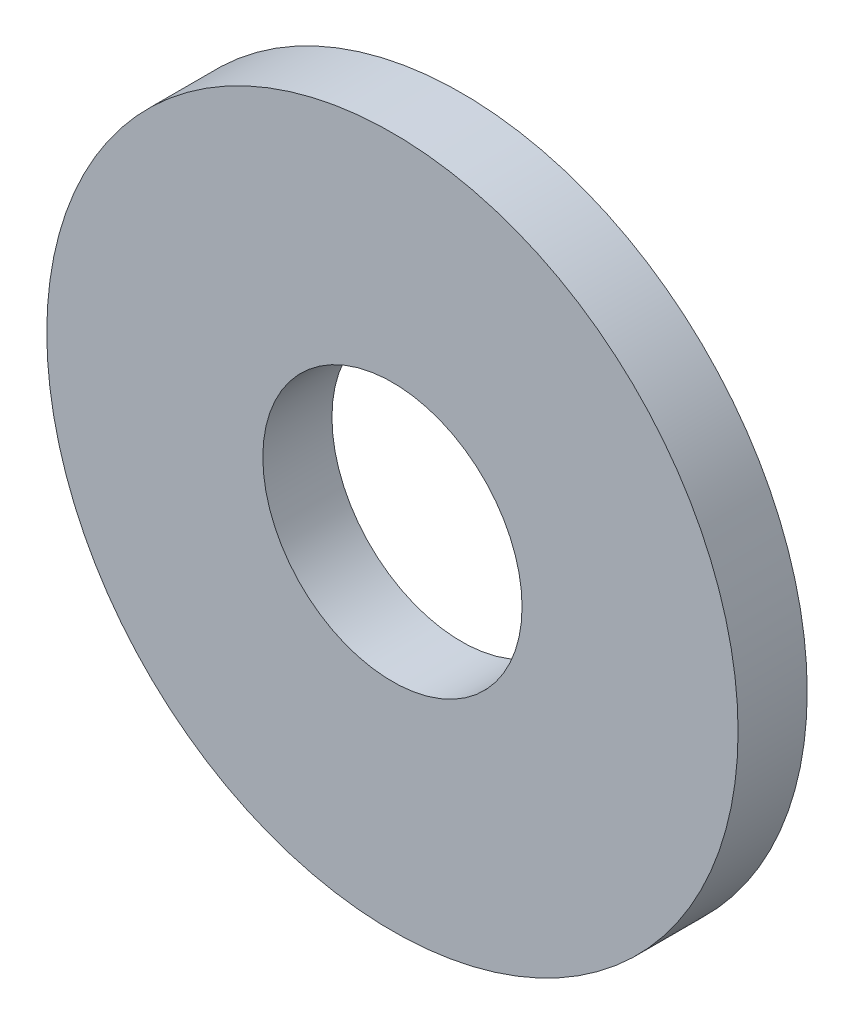
SolidWorks part; units mm, degrees
ref_plane "前视基准面" through (0, 0, 0) normal (0, 0, 1) x (1, 0, 0)
ref_plane "上视基准面" through (0, 0, 0) normal (0, 1, 0) x (1, 0, 0)
ref_plane "右视基准面" through (0, 0, 0) normal (1, 0, 0) x (0, 0, -1)
other "Configuration Table"
sketch "草图2" plane through (0, 0, 0) normal (0, 0, 1) x (1, 0, 0)
  circle A0 centre (0, 0) radius 4
  circle A1 centre (0, 0) radius 1.5
  dimension "D1" = 3
  dimension "D2" = 8
extrude "凸台-拉伸1" add sketch "草图2" along normal blind 0.8
